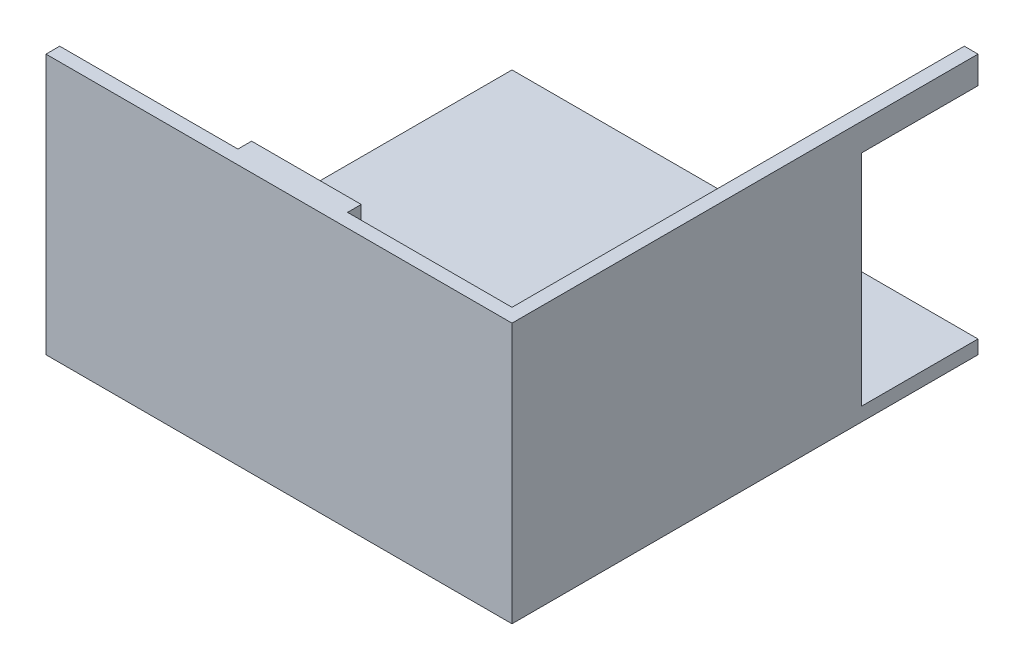
SolidWorks part; units mm, degrees
ref_plane "Front Plane" through (0, 0, 0) normal (0, 0, 1) x (1, 0, 0)
ref_plane "Top Plane" through (0, 0, 0) normal (0, 1, 0) x (1, 0, 0)
ref_plane "Right Plane" through (0, 0, 0) normal (1, 0, 0) x (0, 0, -1)
sketch "Sketch1" plane through (0, 0, 0) normal (0, 1, 0) x (1, 0, 0)
  line L1 (-62.5225, 371.4012) -> (369.2775, 371.4012)
  line L2 (-62.5225, 371.4012) -> (-62.5225, -60.3988)
  line L3 (-62.5225, -60.3988) -> (369.2775, -60.3988)
  line L4 (369.2775, 371.4012) -> (369.2775, -60.3988)
  dimension "D1" = 431.8
  dimension "D2" = 431.8
extrude "Extrude-Thin1" add sketch "Sketch1" along normal blind 228.6 thin
sketch "Sketch2" plane through (0, 0, 0) normal (0, -1, 0) x (1, 0, 0)
  line L1 (369.2775, 60.3988) -> (-62.5225, 60.3988)
  line L2 (369.2775, 60.3988) -> (369.2775, -371.4012)
  line L3 (369.2775, -371.4012) -> (-62.5225, -371.4012)
  line L4 (-62.5225, 60.3988) -> (-62.5225, -371.4012)
extrude "Extrude1" add sketch "Sketch2" along normal blind 12.7
sketch "Sketch3" plane through (0, 0, 0) normal (0, 1, 0) x (-1, 0, 0)
  line L1 (-356.5775, -371.4012) -> (62.5225, -371.4012)
  line L2 (62.5225, -371.4012) -> (62.5225, 47.6988)
  line L3 (62.5225, 47.6988) -> (49.8225, 47.6988)
  line L4 (49.8225, -358.7012) -> (49.8225, 47.6988)
  line L8 (49.8225, -358.7012) -> (-356.5775, -358.7012)
  line L9 (-356.5775, -371.4012) -> (-356.5775, -358.7012)
extrude "Cut-Extrude1" cut sketch "Sketch3" along normal through all
sketch "Sketch4" plane through (0, 0, 0) normal (0, 1, 0) x (-1, 0, 0)
  line L0 (62.5225, 60.3988) -> (-369.2775, 60.3988) construction
  line L1 (-153.3775, 60.3988) -> (-204.1775, 60.3988)
  line L3 (-153.3775, 34.9988) -> (-204.1775, 34.9988)
  line L4 (-204.1775, 60.3988) -> (-204.1775, 34.9988)
  line L6 (-153.3775, 60.3988) -> (-102.5775, 60.3988)
  line L8 (-153.3775, 34.9988) -> (-102.5775, 34.9988)
  line L9 (-102.5775, 60.3988) -> (-102.5775, 34.9988)
  dimension "D1" = 50.8
  dimension "D2" = 25.4
  dimension "D3" = 50.8
extrude "Extrude2" add sketch "Sketch4" along normal up to surface (228.6 mm away) up to face at (221.1108, 228.6, -87.7678)
sketch "Sketch5" plane through (0, 0, 0) normal (0, 1, 0) x (-1, 0, 0)
  line L0 (-369.2775, 60.3988) -> (-369.2775, -371.4012) construction
  line L1 (-356.5775, -371.4012) -> (-369.2775, -371.4012)
  line L2 (-356.5775, -371.4012) -> (-356.5775, -263.4512)
  line L3 (-356.5775, -263.4512) -> (-369.2775, -263.4512)
  line L4 (-369.2775, -371.4012) -> (-369.2775, -263.4512)
  dimension "D1" = 311.15
extrude "Cut-Extrude2" cut sketch "Sketch5" along normal blind 203.2
